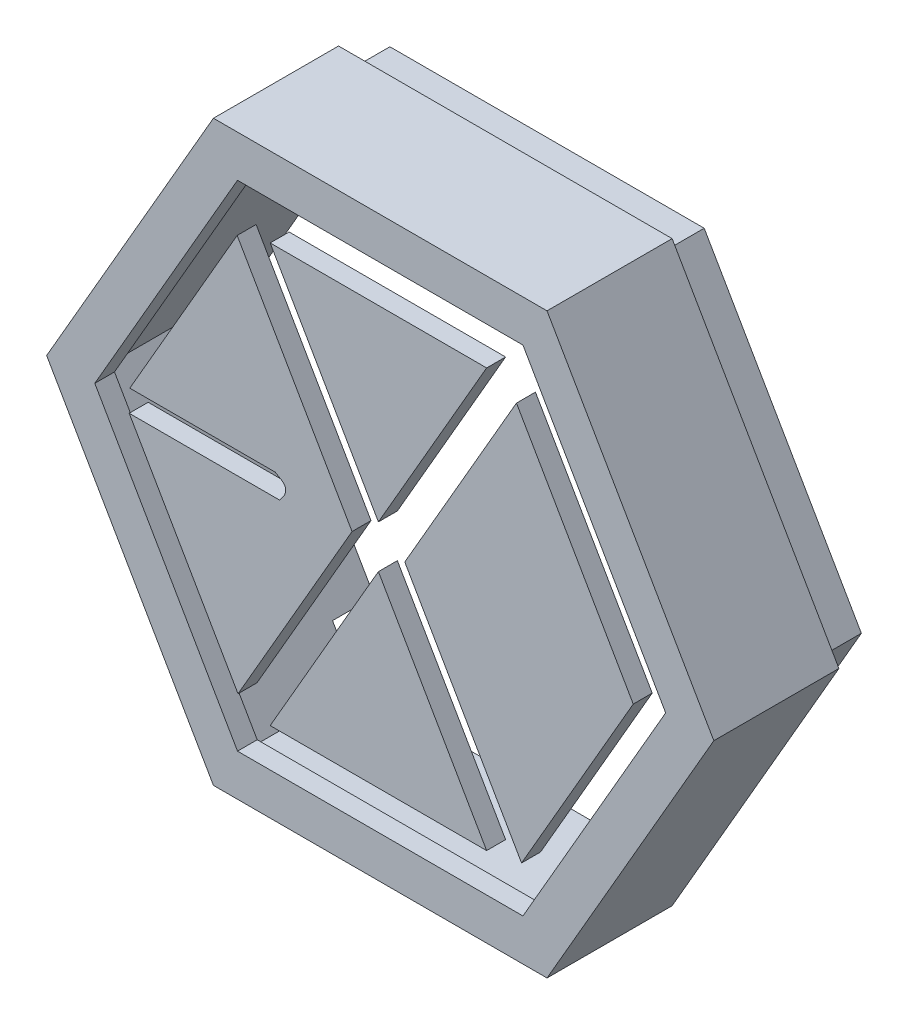
SolidWorks part; units mm, degrees
ref_plane "Front Plane" through (0, 0, 0) normal (0, 0, 1) x (1, 0, 0)
ref_plane "Top Plane" through (0, 0, 0) normal (0, 1, 0) x (1, 0, 0)
ref_plane "Right Plane" through (0, 0, 0) normal (1, 0, 0) x (0, 0, -1)
sketch "Sketch1" plane through (0, 0, 0) normal (0, 0, 1) x (1, 0, 0)
  line L0 (298.5, 788) -> (1492.5, 788) construction
  line L1 (700.7719, 1351.4805) -> (1280.7719, 1351.4805)
  line L2 (1280.7719, 1351.4805) -> (990.7719, 849.1858)
  line L3 (700.7719, 1351.4805) -> (990.7719, 849.1858)
  line L4 (756.685, 791.5255) -> (1083.5931, 791.5255) construction
  line L5 (990.7719, 918.5264) -> (990.7719, 578.4478) construction
  line L6 (580.4677, 141.5704) -> (1415.8737, 141.5704)
  line L7 (1415.8737, 141.5704) -> (1777.5031, 767.931)
  line L8 (1777.5031, 767.931) -> (1388.6291, 1441.4805)
  line L9 (1388.6291, 1441.4805) -> (575.8291, 1441.4805)
  line L10 (612.3198, 1324.6841) -> (920.1391, 791.5255)
  line L11 (920.1391, 791.5255) -> (614.6391, 262.384)
  line L12 (614.6391, 262.384) -> (323.0405, 767.4475)
  line L13 (323.0405, 767.4475) -> (726.261, 767.4475)
  line L14 (714.261, 826.4475) -> (324.6627, 826.4475)
  line L15 (324.6627, 826.4475) -> (612.3198, 1324.6841)
  line L16 (1360.6813, 1309.8876) -> (1673.5801, 767.931)
  line L22 (1061.4048, 791.5255) -> (1374.3036, 249.5689)
  line L24 (1061.4048, 791.5255) -> (1360.6813, 1309.8876)
  line L25 (990.7719, 733.8652) -> (1280.7719, 231.5704)
  line L26 (700.7719, 231.5704) -> (990.7719, 733.8652)
  line L27 (575.8291, 1441.4805) -> (202.8967, 795.5426)
  line L28 (202.8967, 795.5426) -> (580.4677, 141.5704)
  line L30 (1280.7719, 231.5704) -> (700.7719, 231.5704)
  line L35 (1673.5801, 767.931) -> (1374.3036, 249.5689)
  spline S0 degree 3 poles (726.261, 767.4475) (731.261, 775.4475) (738.9729, 782.2952) (741.261, 791.4475) (746.6769, 813.1113) (727.8624, 817.5771) (714.261, 826.4475) knots 0 0 0 0 1 1 1 2 2 2 2
  dimension "D1" = 60
  dimension "D2" = 60
  dimension "D3" = 60
  dimension "D4" = 60
  dimension "D5" = 60
  dimension "D6" = 60
  dimension "D7" = 60
  dimension "D8" = 60
  dimension "D9" = 120
  dimension "D10" = 120
  dimension "D11" = 60
  dimension "D12" = 60
  dimension "D13" = 120
  dimension "D14" = 60
  dimension "D15" = 60
  dimension "D16" = 580
  dimension "D17" = 580
  dimension "D18" = 90
  dimension "D19" = 90
  dimension "D20" = 90
  dimension "D21" = 90
  dimension "D22" = 90
  dimension "D23" = 90
  dimension "D24" = 90
  dimension "D25" = 90
  dimension "D26" = 611
  dimension "D27" = 90
  dimension "D28" = 90
  dimension "D29" = 835.406
  dimension "D30" = 812.8
  dimension "D31" = 777.748
extrude "Boss-Extrude1" add sketch "Sketch1" against normal blind 50.8
scale "Scale2" bodies to scale 101 103 104 102 scale about origin uniform scaling yes scale factor 0.056837
sketch "Sketch2" plane through (0, 0, 0) normal (0, 0, 1) x (1, 0, 0)
  line L1 (104.4582, 44.9488) -> (80.5247, 86.4029)
  line L2 (80.5247, 86.4029) -> (32.6576, 86.4029)
  line L3 (32.6576, 86.4029) -> (8.7241, 44.9488)
  line L4 (8.7241, 44.9488) -> (32.6576, 3.4947)
  line L5 (32.6576, 3.4947) -> (80.5247, 3.4947)
  line L6 (80.5247, 3.4947) -> (104.4582, 44.9488)
  line L7 (107.3911, 44.9488) -> (81.9911, 88.9429)
  line L8 (81.9911, 88.9429) -> (31.1911, 88.9429)
  line L9 (31.1911, 88.9429) -> (5.7911, 44.9488)
  line L10 (5.7911, 44.9488) -> (31.1911, 0.9547)
  line L11 (31.1911, 0.9547) -> (81.9911, 0.9547)
  line L12 (81.9911, 0.9547) -> (107.3911, 44.9488)
  circle A0 centre (56.5911, 44.9488) radius 41.4541 construction
  circle A1 centre (56.5911, 44.9488) radius 43.9941 construction
  dimension "D1" = 50.8
  dimension "D2" = 2.54
extrude "Boss-Extrude2" add sketch "Sketch2" against normal blind 19.05 separate body
sketch "Sketch3" plane through (0, 0, 0) normal (0, 0, 1) x (1, 0, 0)
  line L0 (32.6576, 3.4947) -> (80.5247, 3.4947) construction
  line L1 (101.5253, 44.9488) -> (79.0582, 83.8629)
  line L2 (79.0582, 83.8629) -> (34.1241, 83.8629)
  line L3 (34.1241, 83.8629) -> (11.657, 44.9488)
  line L4 (11.657, 44.9488) -> (34.1241, 6.0347)
  line L5 (34.1241, 6.0347) -> (79.0582, 6.0347)
  line L6 (79.0582, 6.0347) -> (101.5253, 44.9488)
  line L7 (104.4582, 44.9488) -> (80.5247, 86.4029)
  line L8 (80.5247, 86.4029) -> (32.6576, 86.4029)
  line L9 (32.6576, 86.4029) -> (8.7241, 44.9488)
  line L10 (8.7241, 44.9488) -> (32.6576, 3.4947)
  line L11 (32.6576, 3.4947) -> (80.5247, 3.4947)
  line L12 (80.5247, 3.4947) -> (104.4582, 44.9488)
  line L14 (80.5247, 86.4029) -> (32.6576, 86.4029) construction
  line L15 (80.5247, 3.4947) -> (104.4582, 44.9488) construction
  circle A0 centre (56.5911, 44.9488) radius 38.9141 construction
  circle A1 centre (56.5911, 44.9488) radius 41.4541 construction
  dimension "D1" = 2.54
extrude "Boss-Extrude3" add sketch "Sketch3" against normal blind 25.4
sketch "Sketch4" plane through (0, 0, 0) normal (0, 0, 1) x (1, 0, 0)
  line L1 (100.0588, 44.9488) -> (78.325, 82.5929)
  line L2 (78.325, 82.5929) -> (34.8573, 82.5929)
  line L3 (34.8573, 82.5929) -> (13.1235, 44.9488)
  line L4 (13.1235, 44.9488) -> (34.8573, 7.3047)
  line L5 (34.8573, 7.3047) -> (78.325, 7.3047)
  line L6 (78.325, 7.3047) -> (100.0588, 44.9488)
  line L10 (101.5253, 44.9488) -> (79.0582, 83.8629)
  line L11 (79.0582, 83.8629) -> (34.1241, 83.8629)
  line L12 (34.1241, 83.8629) -> (11.657, 44.9488)
  line L13 (11.657, 44.9488) -> (34.1241, 6.0347)
  line L14 (34.1241, 6.0347) -> (79.0582, 6.0347)
  line L15 (79.0582, 6.0347) -> (101.5253, 44.9488)
  circle A0 centre (56.5911, 44.9488) radius 37.6441 construction
  circle A1 centre (56.5911, 44.9488) radius 38.9141 construction
  dimension "D1" = 1.27
extrude "Boss-Extrude4" add sketch "Sketch4" against normal blind 3
sketch "Sketch5" plane through (0, 0, 0) normal (0, 1, 0) x (1, 0, 0)
  line L0 (18.4911, -9.2885) -> (18.4911, 33.9538) construction
  line L1 (94.6911, -9.2885) -> (94.6911, 33.9538) construction
  line L2 (5.7911, 19.05) -> (5.7911, 0) construction
  line L3 (31.1911, 19.05) -> (31.1911, 0) construction
  line L4 (81.9911, 19.05) -> (81.9911, 0) construction
  line L5 (107.3911, 19.05) -> (107.3911, 0) construction
  line L6 (5.7911, 19.05) -> (31.1911, 19.05) construction
  line L7 (18.4911, 19.05) -> (94.6911, 19.05)
  line L8 (18.4911, 19.05) -> (18.4911, 25.4)
  line L9 (18.4911, 25.4) -> (94.6911, 25.4)
  line L10 (94.6911, 19.05) -> (94.6911, 25.4)
  line L11 (80.5247, 25.4) -> (104.4582, 25.4) construction
extrude "Cut-Extrude1" cut sketch "Sketch5" along normal blind 12.7
